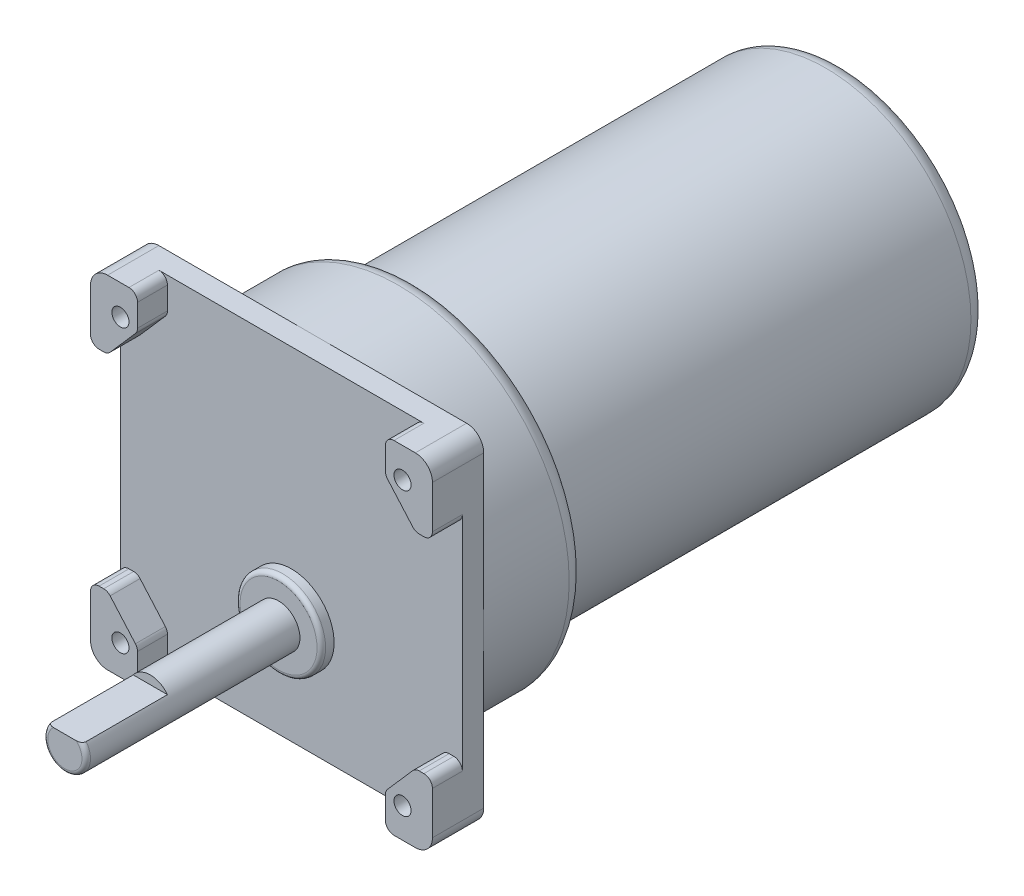
SolidWorks part; units mm, degrees
ref_plane "Front Plane" through (0, 0, 0) normal (0, 0, 1) x (1, 0, 0)
ref_plane "Top Plane" through (0, 0, 0) normal (0, 1, 0) x (1, 0, 0)
ref_plane "Right Plane" through (0, 0, 0) normal (1, 0, 0) x (0, 0, -1)
sketch "Sketch1" plane through (0, 0, 0) normal (0, 0, 1) x (1, 0, 0)
  circle A0 centre (0, 0) radius 40
  dimension "D1" = 80
extrude "Boss-Extrude1" add sketch "Sketch1" along normal blind 24
sketch "Sketch2" plane through (0, 0, 24) normal (0, 0, 1) x (1, 0, 0)
  line L0 (0, 0) -> (13.9236, 0) construction
  line L1 (-40, -40) -> (40, -40)
  line L2 (-40, -40) -> (-40, 40)
  line L3 (-40, 40) -> (40, 40)
  line L4 (40, -40) -> (40, 40)
  line L5 (-40, -40) -> (40, 40) construction
  line L6 (-40, 40) -> (40, -40) construction
  circle A0 centre (0, 0) radius 40 construction
  circle A1 centre (33, -33) radius 2
  circle A2 centre (-33, 33) radius 2
  circle A3 centre (33, 33) radius 2
  circle A4 centre (-33, -33) radius 2
  point P0 (0, 0)
  dimension "D1" = 4
  dimension "D2" = 66
extrude "Boss-Extrude2" add sketch "Sketch2" along normal blind 5
fillet "Fillet1" radius 4 4 edges at (-40, 40, 26.5) (40, 40, 26.5) (40, -40, 26.5) (-40, -40, 26.5)
sketch "Sketch3" plane through (0, 0, 0) normal (0, 0, -1) x (-1, 0, 0)
  circle A0 centre (0, 0) radius 34
  dimension "D1" = 68
extrude "Boss-Extrude3" add sketch "Sketch3" along normal blind 100
fillet "Fillet2" radius 4 2 edges at (40, 0, 0) (-34, 0, -100)
sketch "Sketch4" plane through (0, 0, 29) normal (0, 0, 1) x (1, 0, 0)
  line L0 (-36, -40) -> (36, -40) construction
  line L1 (0, -15) -> (0, -33) construction
  line L2 (0, -33) -> (-33, -33) construction
  line L3 (0, -33) -> (33, -33) construction
  circle A0 centre (0, -15) radius 10
  point P4 (0, -15)
  point P9 (0, -5)
  point P10 (0, -40)
  dimension "D2" = 20
  dimension "D3" = 35
extrude "Boss-Extrude4" add sketch "Sketch4" along normal blind 3
sketch "Sketch5" plane through (0, 0, 32) normal (0, 0, 1) x (1, 0, 0)
  circle A0 centre (0, -15) radius 5
  dimension "D1" = 10
extrude "Boss-Extrude5" add sketch "Sketch5" along normal blind 50
fillet "Fillet3" radius 1 1 edges at (10, -15, 32)
fillet "Fillet4" radius 1 1 edges at (5, -15, 82)
sketch "Sketch6" plane through (-40, 0, 0) normal (-1, 0, 0) x (0, 0, 1)
  line L0 (81, -10) -> (32, -10) construction
  line L1 (62, -10) -> (88.9791, -10)
  line L2 (62, -10) -> (62, -12)
  line L3 (62, -12) -> (88.9791, -12)
  line L4 (88.9791, -10) -> (88.9791, -12)
  line L5 (82, -19) -> (82, -11) construction
  dimension "D1" = 2
  dimension "D2" = 20
extrude "Cut-Extrude1" cut sketch "Sketch6" against normal through all both and the other way through all
sketch "Sketch8" plane through (0, 0, 29) normal (0, 0, 1) x (1, 0, 0)
  line L0 (-40, 24) -> (-36, 24)
  line L1 (-40, 36) -> (-40, -36) construction
  line L2 (-36, 24) -> (-29, 32)
  line L3 (-29, 32) -> (-29, 40)
  line L4 (36, 40) -> (-36, 40) construction
  line L5 (0, -7.7134) -> (0, 18.0911) construction
  line L6 (-8.3596, 0) -> (10.225, 0) construction
  line L7 (-40, 36) -> (-40, 24)
  line L8 (-29, 40) -> (-36, 40)
  line L9 (29, 40) -> (36, 40)
  line L10 (40, 36) -> (40, 24)
  line L11 (29, 32) -> (29, 40)
  line L12 (36, 24) -> (29, 32)
  line L13 (40, 24) -> (36, 24)
  line L14 (40, -24) -> (36, -24)
  line L15 (36, -24) -> (29, -32)
  line L16 (29, -32) -> (29, -40)
  line L17 (40, -36) -> (40, -24)
  line L18 (29, -40) -> (36, -40)
  line L19 (-29, -40) -> (-36, -40)
  line L20 (-40, -36) -> (-40, -24)
  line L21 (-29, -32) -> (-29, -40)
  line L22 (-36, -24) -> (-29, -32)
  line L23 (-40, -24) -> (-36, -24)
  arc A0 (-36, 40) -> (-40, 36) centre (-36, 36) ccw construction
  arc A1 (-36, 40) -> (-40, 36) centre (-36, 36) ccw
  arc A2 (36, 40) -> (40, 36) centre (36, 36) cw
  arc A3 (36, -40) -> (40, -36) centre (36, -36) ccw
  arc A4 (-36, -40) -> (-40, -36) centre (-36, -36) cw
  line M6 (36, 40) -> (-36, 40)
  arc M7 (-36, 40) -> (-40, 36) centre (-36, 36) ccw
  line M8 (-40, 36) -> (-40, -36)
  arc M9 (-40, -36) -> (-36, -40) centre (-36, -36) ccw
  line M10 (-36, -40) -> (36, -40)
  arc M11 (36, -40) -> (40, -36) centre (36, -36) ccw
  line M12 (40, -36) -> (40, 36)
  arc M13 (40, 36) -> (36, 40) centre (36, 36) ccw
  circle M14 centre (33, -33) radius 2
  circle M15 centre (-33, 33) radius 2
  circle M16 centre (33, 33) radius 2
  circle M17 centre (-33, -33) radius 2
  dimension "D1" = 16
  dimension "D2" = 11
  dimension "D3" = 4
  dimension "D4" = 8
extrude "Boss-Extrude6" add sketch "Sketch8" along normal blind 7 contours L23 L21 L22 M8 M9 M10 M17 | L15 L16 L14 M10 M11 M12 M14 | L2 L3 L0 M6 M7 M8 M15 | L13 L11 L12 M12 M13 M6 M16
fillet "Fillet5" radius 2 16 edges at (36, -24, 32.5) (29, -32, 32.5) (-36, -24, 32.5) (-29, -32, 32.5) (29, 32, 32.5) (36, 24, 32.5) (-29, 32, 32.5) (-36, 24, 32.5) (29, 40, 32.5) (40, 24, 32.5) (-29, 40, 32.5) (-40, 24, 32.5) (-29, -40, 32.5) (29, -40, 32.5) (40, -24, 32.5) (-40, -24, 32.5)
